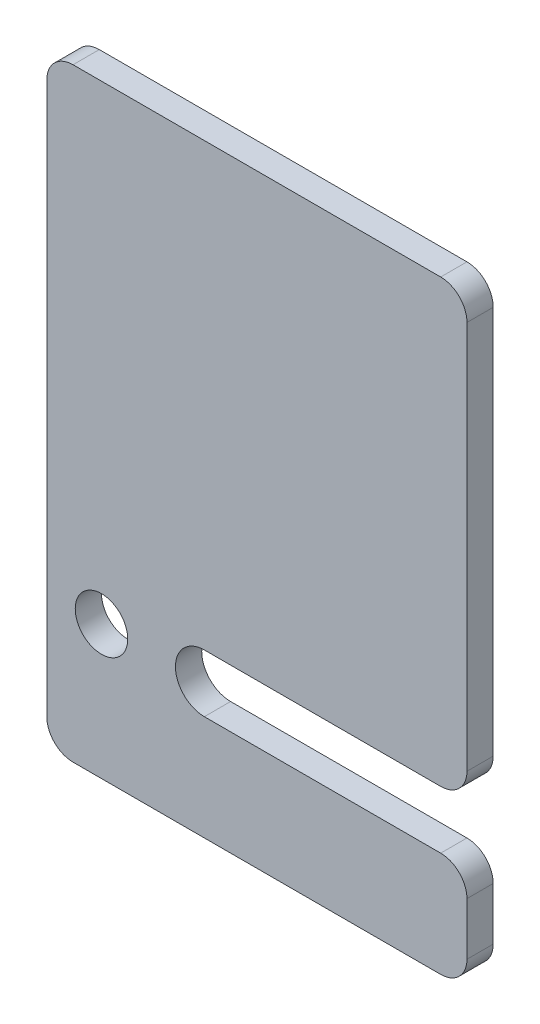
SolidWorks part; units mm, degrees
ref_plane "Plan de face" through (0, 0, 0) normal (0, 0, 1) x (1, 0, 0)
ref_plane "Plan de dessus" through (0, 0, 0) normal (0, 1, 0) x (1, 0, 0)
ref_plane "Plan de droite" through (0, 0, 0) normal (1, 0, 0) x (0, 0, -1)
sketch "Esquisse1" plane through (0, 0, 0) normal (0, 0, 1) x (1, 0, 0)
  line L0 (80, 110) -> (80, 36)
  line L1 (5, 0) -> (75, 0)
  line L2 (0, 5) -> (0, 110)
  line L3 (5, 115) -> (75, 115)
  line L4 (80, 0) -> (80, 115) construction
  line L5 (75, 31) -> (30, 31)
  line L7 (30, 20) -> (75, 20)
  line L9 (80, 15) -> (80, 5)
  arc A0 (5, 0) -> (0, 5) centre (5, 5) cw
  arc A1 (30, 31) -> (30, 20) centre (30, 25.5) ccw
  arc A2 (75, 20) -> (80, 15) centre (75, 15) cw
  arc A3 (75, 31) -> (80, 36) centre (75, 36) ccw
  arc A4 (80, 5) -> (75, 0) centre (75, 5) cw
  arc A6 (75, 115) -> (80, 110) centre (75, 110) cw
  arc A7 (0, 110) -> (5, 115) centre (5, 110) cw
  point P11 (0, 0)
  point P14 (80, 20)
  point P18 (80, 31)
  point P23 (80, 20)
  point P26 (80, 31)
  point P32 (0, 115)
  dimension "D6" = 5
  dimension "D5" = 50
  dimension "D4" = 5.5
  dimension "D7" = 5
  dimension "D8" = 5
  dimension "D1" = 115
  dimension "D2" = 80
  dimension "D3" = 20
extrude "Boss.-Extru.1" add sketch "Esquisse1" along normal blind 5
sketch "Esquisse2" plane through (0, 0, 0) normal (0, 0, -1) x (-1, 0, 0)
  line L2 (-10.4158, 25.5) -> (-0.4158, 25.5) construction
  circle A0 centre (-10.4158, 25.5) radius 5
  point P2 (0, 0)
  dimension "D1" = 10
  dimension "D2" = 10
sketch "Esquisse3" plane through (0, 0, 0) normal (0, 0, -1) x (-1, 0, 0)
  circle A0 centre (-10.4158, 25.5) radius 5
extrude "Enlèv. mat.-Extru.1" cut sketch "Esquisse3" against normal blind 10
